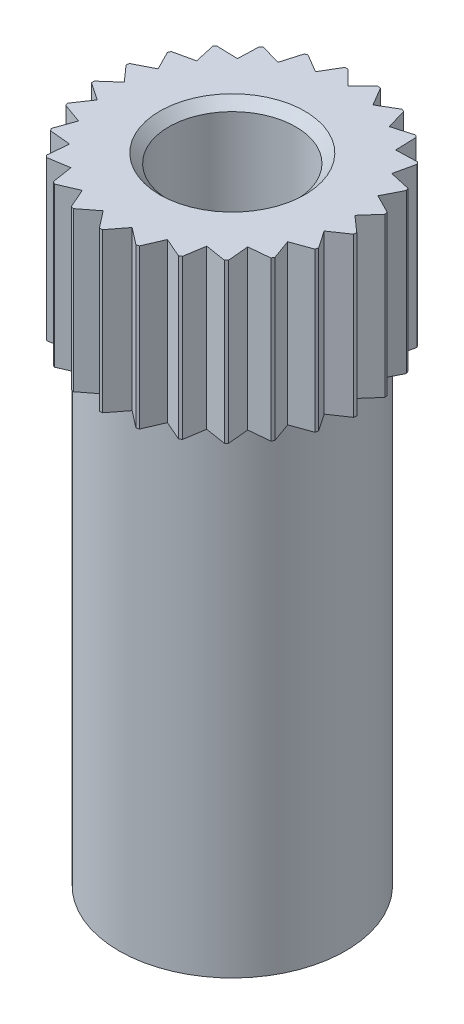
SolidWorks part; units mm, degrees
ref_plane "Front" through (0, 0, 0) normal (0, 0, 1) x (1, 0, 0)
ref_plane "Top" through (0, 0, 0) normal (0, 1, 0) x (1, 0, 0)
ref_plane "Right" through (0, 0, 0) normal (1, 0, 0) x (0, 0, -1)
sketch "Эскиз1" plane through (0, 0, 0) normal (0, 1, 0) x (1, 0, 0)
  circle A0 centre (0, 0) radius 2.9
  dimension "D1" = 5.8
extrude "Бобышка-Вытянуть1" add sketch "Эскиз1" along normal blind 3.5
sketch "Эскиз2" plane through (0, 0, 0) normal (0, -1, 0) x (1, 0, 0)
  circle A0 centre (0, 0) radius 2.5
  dimension "D1" = 5
extrude "Бобышка-Вытянуть2" add sketch "Эскиз2" along normal blind 10.5
sketch "Эскиз3" plane through (0, 3.5, 0) normal (0, 1, 0) x (1, 0, 0)
  line L0 (0, 2.55) -> (-0.3665, 2.9165)
  line L1 (-0.3665, 2.9165) -> (0.3665, 2.9165)
  line L2 (0.3665, 2.9165) -> (0, 2.55)
  line L3 (0.6342, 2.4699) -> (0.3703, 2.916)
  line L4 (0.3703, 2.916) -> (1.0803, 2.7337)
  line L5 (1.0803, 2.7337) -> (0.6342, 2.4699)
  line L6 (1.2285, 2.2346) -> (1.0839, 2.7323)
  line L7 (1.0839, 2.7323) -> (1.7262, 2.3792)
  line L8 (1.7262, 2.3792) -> (1.2285, 2.2346)
  line L9 (1.7456, 1.8589) -> (1.7293, 2.3769)
  line L10 (1.7293, 2.3769) -> (2.2636, 1.8752)
  line L11 (2.2636, 1.8752) -> (1.7456, 1.8589)
  line L12 (2.153, 1.3664) -> (2.2661, 1.8722)
  line L13 (2.2661, 1.8722) -> (2.6589, 1.2533)
  line L14 (2.6589, 1.2533) -> (2.153, 1.3664)
  line L15 (2.4252, 0.788) -> (2.6605, 1.2498)
  line L16 (2.6605, 1.2498) -> (2.887, 0.5527)
  line L17 (2.887, 0.5527) -> (2.4252, 0.788)
  line L18 (2.545, 0.1601) -> (2.8877, 0.5489)
  line L19 (2.8877, 0.5489) -> (2.9338, -0.1826)
  line L20 (2.9338, -0.1826) -> (2.545, 0.1601)
  line L21 (2.5048, -0.4778) -> (2.9335, -0.1865)
  line L22 (2.9335, -0.1865) -> (2.7962, -0.9065)
  line L23 (2.7962, -0.9065) -> (2.5048, -0.4778)
  line L24 (2.3073, -1.0857) -> (2.795, -0.9102)
  line L25 (2.795, -0.9102) -> (2.4829, -1.5734)
  line L26 (2.4829, -1.5734) -> (2.3073, -1.0857)
  line L27 (1.9648, -1.6254) -> (2.4808, -1.5767)
  line L28 (2.4808, -1.5767) -> (2.0136, -2.1414)
  line L29 (2.0136, -2.1414) -> (1.9648, -1.6254)
  line L30 (1.4989, -2.063) -> (2.0108, -2.1441)
  line L31 (2.0108, -2.1441) -> (1.4178, -2.5749)
  line L32 (1.4178, -2.5749) -> (1.4989, -2.063)
  line L33 (0.9387, -2.3709) -> (1.4144, -2.5768)
  line L34 (1.4144, -2.5768) -> (0.7329, -2.8466)
  line L35 (0.7329, -2.8466) -> (0.9387, -2.3709)
  line L36 (0.3196, -2.5299) -> (0.7291, -2.8476)
  line L37 (0.7291, -2.8476) -> (0.0019, -2.9394)
  line L38 (0.0019, -2.9394) -> (0.3196, -2.5299)
  line L39 (-0.3196, -2.5299) -> (-0.0019, -2.9394)
  line L40 (-0.0019, -2.9394) -> (-0.7291, -2.8476)
  line L41 (-0.7291, -2.8476) -> (-0.3196, -2.5299)
  line L42 (-0.9387, -2.3709) -> (-0.7329, -2.8466)
  line L43 (-0.7329, -2.8466) -> (-1.4144, -2.5768)
  line L44 (-1.4144, -2.5768) -> (-0.9387, -2.3709)
  line L45 (-1.4989, -2.063) -> (-1.4178, -2.5749)
  line L46 (-1.4178, -2.5749) -> (-2.0108, -2.1441)
  line L47 (-2.0108, -2.1441) -> (-1.4989, -2.063)
  line L48 (-1.9648, -1.6254) -> (-2.0136, -2.1414)
  line L49 (-2.0136, -2.1414) -> (-2.4808, -1.5767)
  line L50 (-2.4808, -1.5767) -> (-1.9648, -1.6254)
  line L51 (-2.3073, -1.0857) -> (-2.4829, -1.5734)
  line L52 (-2.4829, -1.5734) -> (-2.795, -0.9102)
  line L53 (-2.795, -0.9102) -> (-2.3073, -1.0857)
  line L54 (-2.5048, -0.4778) -> (-2.7962, -0.9065)
  line L55 (-2.7962, -0.9065) -> (-2.9335, -0.1865)
  line L56 (-2.9335, -0.1865) -> (-2.5048, -0.4778)
  line L57 (-2.545, 0.1601) -> (-2.9338, -0.1826)
  line L58 (-2.9338, -0.1826) -> (-2.8877, 0.5489)
  line L59 (-2.8877, 0.5489) -> (-2.545, 0.1601)
  line L60 (-2.4252, 0.788) -> (-2.887, 0.5527)
  line L61 (-2.887, 0.5527) -> (-2.6605, 1.2498)
  line L62 (-2.6605, 1.2498) -> (-2.4252, 0.788)
  line L63 (-2.153, 1.3664) -> (-2.6589, 1.2533)
  line L64 (-2.6589, 1.2533) -> (-2.2661, 1.8722)
  line L65 (-2.2661, 1.8722) -> (-2.153, 1.3664)
  line L66 (-1.7456, 1.8589) -> (-2.2636, 1.8752)
  line L67 (-2.2636, 1.8752) -> (-1.7293, 2.3769)
  line L68 (-1.7293, 2.3769) -> (-1.7456, 1.8589)
  line L69 (-1.2285, 2.2346) -> (-1.7262, 2.3792)
  line L70 (-1.7262, 2.3792) -> (-1.0839, 2.7323)
  line L71 (-1.0839, 2.7323) -> (-1.2285, 2.2346)
  line L72 (-0.6342, 2.4699) -> (-1.0803, 2.7337)
  line L73 (-1.0803, 2.7337) -> (-0.3703, 2.916)
  line L74 (-0.3703, 2.916) -> (-0.6342, 2.4699)
  circle A0 centre (0, 0) radius 2.55 construction
  point P5 (-0.2904, 2.8854)
  point P81 (0, 0)
  dimension "D1" = 5.1
  dimension "D2" = 90
  dimension "D3" = 25
extrude "Вырез-Вытянуть1" cut sketch "Эскиз3" against normal blind 4
hole_wizard "Сверло под метчик  спиральное M32" positions "Эскиз8" profile "Эскиз7" hole size "M3x0.5" standard "Din"
sketch "Эскиз8" plane through (0, 3.5, 0) normal (0, 1, 0) x (1, 0, 0)
  point P0 (0, 0)
sketch "Эскиз7" plane through (0, 3.5, 0) normal (1, 0, 0) x (0, 0, 1)
  line L0 (0, 0) -> (0, 7.4)
  line L1 (0, 7.4) -> (1.4, 6)
  line L2 (1.4, 6) -> (1.4, 0.2)
  line L3 (1.4, 0.2) -> (1.6, 0)
  line L5 (1.6, 0) -> (0, 0)
  line L6 (-1.4, 0.2) -> (-1.6, 0) construction
  line L10 (0, 7.4) -> (-1.4, 6) construction
  line L11 (0, -6.35) -> (0, 107.95) construction
  dimension "Диаметр отверстия" = 2.8
  dimension "Глубина отверстия" = 6
  dimension "Диаметр передней зенковки" = 3.2
  dimension "Угол передней зенковки" = 90
  dimension "Угол заточки сверла" = 90
